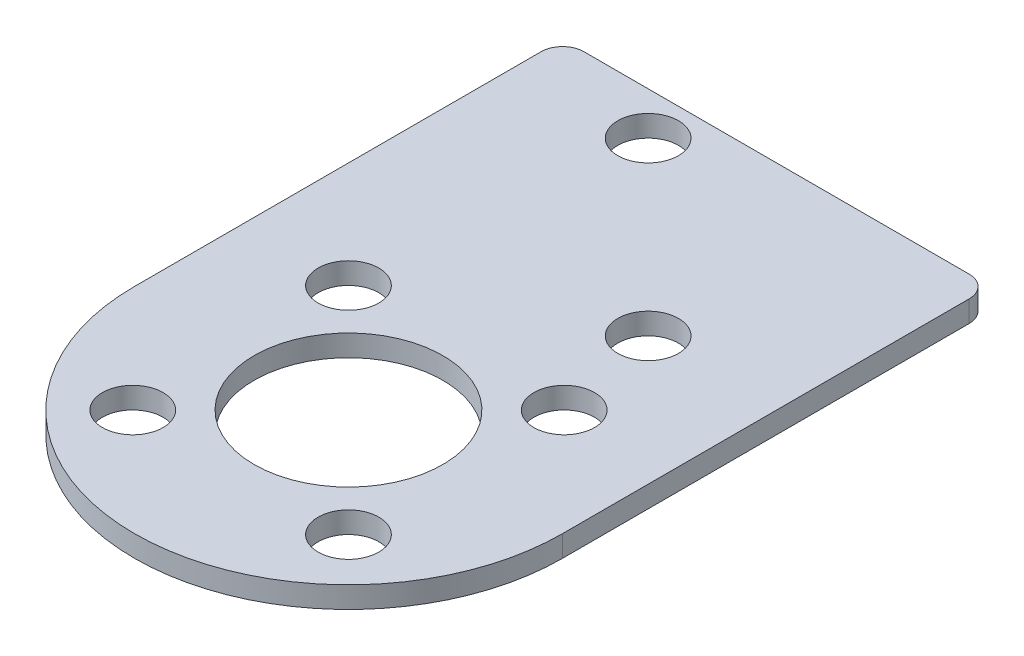
SolidWorks part; units mm, degrees
ref_plane "Front Plane" through (0, 0, 0) normal (0, 0, 1) x (1, 0, 0)
ref_plane "Top Plane" through (0, 0, 0) normal (0, 1, 0) x (1, 0, 0)
ref_plane "Right Plane" through (0, 0, 0) normal (1, 0, 0) x (0, 0, -1)
sketch "Sketch1" plane through (0, 0, 0) normal (0, 1, 0) x (1, 0, 0)
  line L0 (-15.875, 12.7) -> (15.875, 12.7) construction
  line L1 (-15.875, 0) -> (15.875, 0)
  line L2 (-15.875, 0) -> (-15.875, 30.1625)
  line L3 (-14.2875, 31.75) -> (14.2875, 31.75)
  line L4 (15.875, 0) -> (15.875, 30.1625)
  circle A0 centre (0, 0) radius 7
  circle A1 centre (-8, 8) radius 2.25
  circle A3 centre (8, 8) radius 2.25
  circle A4 centre (8, -8) radius 2.25
  circle A5 centre (-8, -8) radius 2.25
  arc A6 (-15.875, 0) -> (15.875, 0) centre (0, 0) ccw
  circle A7 centre (-6.35, 28.575) radius 2.25
  circle A8 centre (6.35, 15.875) radius 2.25
  arc A9 (14.2875, 31.75) -> (15.875, 30.1625) centre (14.2875, 30.1625) cw
  arc A10 (-15.875, 30.1625) -> (-14.2875, 31.75) centre (-14.2875, 30.1625) cw
  point P15 (0, 0)
  point P20 (0, 0)
  point P25 (15.875, 31.75)
  point P28 (-15.875, 31.75)
  dimension "D1" = 14
  dimension "D2" = 4.5
  dimension "D12" = 1.5875
  dimension "D3" = 16
  dimension "D5" = 31.75
  dimension "D6" = 12.7
  dimension "D7" = 19.05
  dimension "D8" = 6.35
  dimension "D9" = 6.35
  dimension "D10" = 3.175
  dimension "D11" = 3.175
  dimension "D4" = 4
extrude "Boss-Extrude1" add sketch "Sketch1" along normal blind 1.5875 contours L2 L0 L4 L3 A7 A8 | L0 L2 L1 A0 L4 A3 A1 | L1 A6 A0 A4 A5
